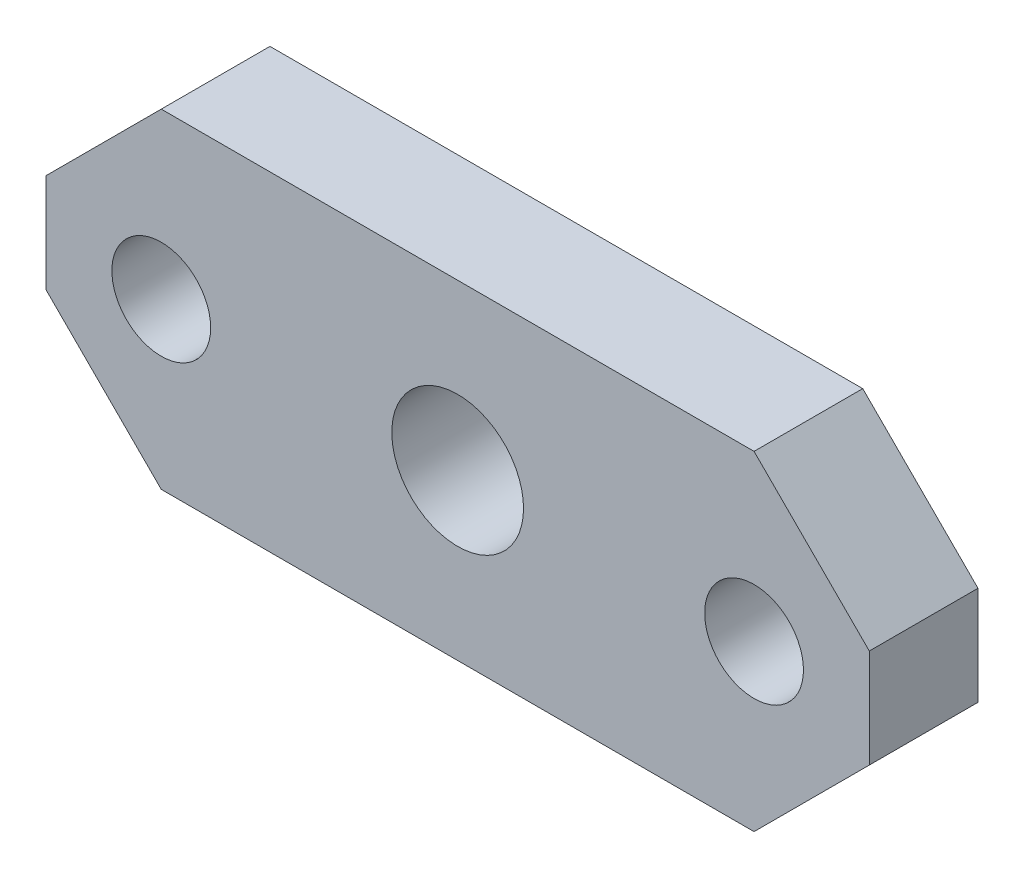
SolidWorks part; units mm, degrees
ref_plane "Front Plane" through (0, 0, 0) normal (0, 0, 1) x (1, 0, 0)
ref_plane "Top Plane" through (0, 0, 0) normal (0, 1, 0) x (1, 0, 0)
ref_plane "Right Plane" through (0, 0, 0) normal (1, 0, 0) x (0, 0, -1)
sketch "Sketch1" plane through (0, 0, 0) normal (0, 0, 1) x (1, 0, 0)
  line L1 (-110.2417, 51.8602) -> (139.7583, 51.8602)
  line L2 (-110.2417, 51.8602) -> (-110.2417, -48.1398)
  line L3 (-110.2417, -48.1398) -> (139.7583, -48.1398)
  line L4 (139.7583, 51.8602) -> (139.7583, -48.1398)
  dimension "D1" = 250
  dimension "D2" = 100
extrude "Boss-Extrude1" add sketch "Sketch1" along normal blind 33 contours L1 L4 L3 L2
chamfer "Chamfer1" distance 35 angle 45 4 edges at (139.7583, 51.8602, 16.5) (139.7583, -48.1398, 16.5) (-110.2417, 51.8602, 16.5) (-110.2417, -48.1398, 16.5)
sketch "Sketch2" plane through (0, 0, 33) normal (0, 0, 1) x (1, 0, 0)
  line L0 (139.7583, 16.8602) -> (139.7583, -13.1398) construction
  line L1 (-75.2417, 51.8602) -> (104.7583, 51.8602) construction
  circle A0 centre (14.7583, 1.8602) radius 20
  point P2 (0, 0)
  dimension "D3" = 40
  dimension "D1" = 125
  dimension "D2" = 50
extrude "Cut-Extrude1" cut sketch "Sketch2" against normal blind 35
sketch "Sketch3" plane through (0, 0, 33) normal (0, 0, 1) x (1, 0, 0)
  line L0 (-75.2417, -48.1398) -> (104.7583, -48.1398) construction
  line L1 (139.7583, 16.8602) -> (139.7583, -13.1398) construction
  circle A0 centre (104.7583, 1.8602) radius 15
  dimension "D1" = 30
  dimension "D2" = 50
  dimension "D3" = 35
extrude "Cut-Extrude2" cut sketch "Sketch3" against normal up to next (33 mm away)
pattern_linear "LPattern1" count 2 spacing 180 along (-1, 0, 0) of "Cut-Extrude2"
